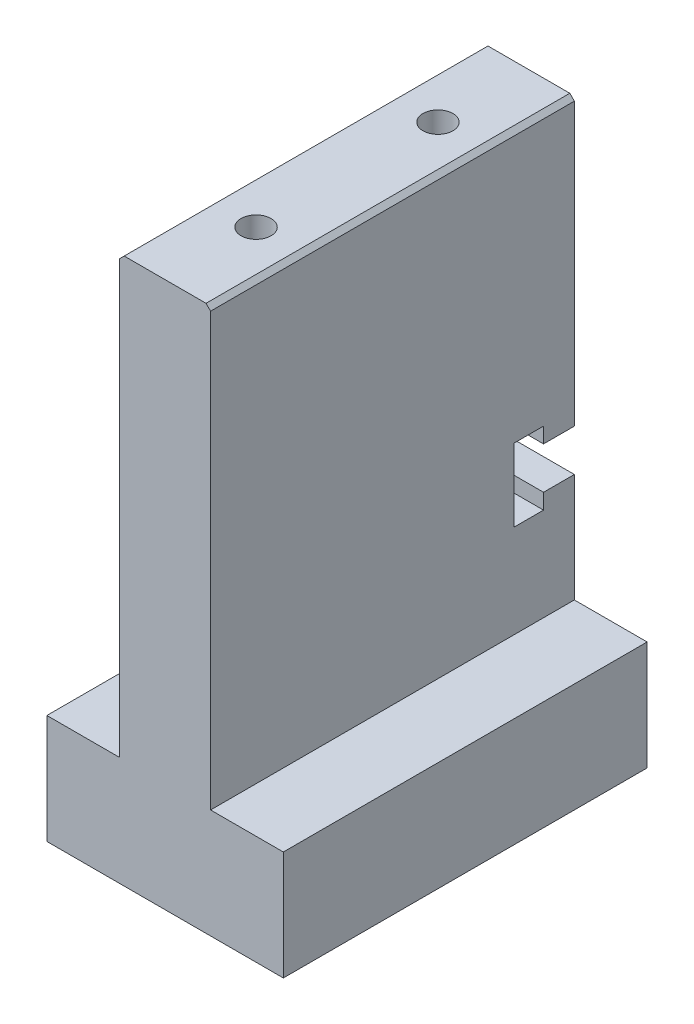
SolidWorks part; units mm, degrees
ref_plane "Front Plane" through (0, 0, 0) normal (0, 0, 1) x (1, 0, 0)
ref_plane "Top Plane" through (0, 0, 0) normal (0, 1, 0) x (1, 0, 0)
ref_plane "Right Plane" through (0, 0, 0) normal (1, 0, 0) x (0, 0, -1)
sketch "Sketch1" plane through (0, 0, 0) normal (0, 0, 1) x (1, 0, 0)
  line L1 (-10.8894, 5.2918) -> (15.1106, 5.2918)
  line L2 (-10.8894, 5.2918) -> (-10.8894, -6.7082)
  line L3 (-10.8894, -6.7082) -> (15.1106, -6.7082)
  line L4 (15.1106, 5.2918) -> (15.1106, -6.7082)
  dimension "D1" = 26
  dimension "D2" = 12
extrude "Boss-Extrude1" add sketch "Sketch1" along normal blind 40
sketch "Sketch2" plane through (0, 5.2918, 0) normal (0, 1, 0) x (1, 0, 0)
  line L0 (15.1106, 0) -> (-10.8894, 0) construction
  line L1 (-2.8894, 0) -> (7.1106, 0)
  line L2 (-2.8894, 0) -> (-2.8894, -40)
  line L3 (-2.8894, -40) -> (7.1106, -40)
  line L4 (7.1106, 0) -> (7.1106, -40)
  line L5 (15.1106, -40) -> (-10.8894, -40) construction
  line L6 (-10.8894, -40) -> (-10.8894, 0) construction
  dimension "D1" = 8
  dimension "D2" = 10
extrude "Boss-Extrude2" add sketch "Sketch2" along normal blind 48
sketch "Sketch3" plane through (-2.8894, 0, 0) normal (-1, 0, 0) x (0, 0, 1)
  line L0 (0, 53.2918) -> (0, 5.2918) construction
  line L1 (0, 21.8418) -> (3.3898, 21.8418)
  line L2 (0, 21.8418) -> (0, 17.2418)
  line L3 (0, 17.2418) -> (3.3898, 17.2418)
  line L4 (0, 53.2918) -> (40, 53.2918) construction
  line L5 (3.3898, 17.2418) -> (3.3898, 15.5418)
  line L6 (3.3898, 23.5418) -> (6.6639, 23.5418)
  line L7 (3.3898, 23.5418) -> (3.3898, 21.8418)
  line L8 (3.3898, 15.5418) -> (6.6639, 15.5418)
  line L9 (6.6639, 23.5418) -> (6.6639, 15.5418)
  dimension "D1" = 29.75
  dimension "D2" = 31.45
  dimension "D3" = 36.05
  dimension "D4" = 37.75
extrude "Cut-Extrude1" cut sketch "Sketch3" against normal blind 48
hole_wizard "M3 Tapped Hole1" positions "Sketch5" profile "Sketch4" tap size "M3" standard "ISO"
sketch "Sketch5" plane through (0, 0, 0) normal (0, 0, -1) x (-1, 0, 0)
  line L0 (10.8894, -6.7082) -> (-15.1106, -6.7082) construction
  line L1 (-15.1106, -6.7082) -> (-15.1106, 5.2918) construction
  line L2 (-7.1106, 53.2918) -> (2.8894, 53.2918) construction
  line L3 (-7.1106, 53.2918) -> (-7.1106, 21.8418) construction
  point P0 (-9.1106, -0.7082)
  point P2 (4.8894, -0.7082)
  point P4 (-2.1106, 51.2918)
  dimension "D1" = 6
  dimension "D2" = 6
  dimension "D3" = 6
  dimension "D4" = 14
  dimension "D5" = 2
  dimension "D6" = 5
sketch "Sketch4" plane through (9.1106, -0.7082, 0) normal (1, 0, 0) x (0, 1, 0)
  line L0 (0, 0) -> (0, 6.7511)
  line L1 (0, 6.7511) -> (1.25, 6)
  line L2 (1.25, 6) -> (1.25, 0)
  line L5 (1.25, 0) -> (0, 0)
  line L10 (0, 6.7511) -> (-1.25, 6) construction
  line L11 (0, -6.35) -> (0, 107.95) construction
  dimension "Tap Drill Dia." = 2.5
  dimension "Tap Drill Depth" = 6
  dimension "Drill Angle" = 118
cosmetic thread "Hole Thread1" parameters "D1"=6, "D2"=3
cosmetic thread "Hole Thread2" parameters "D1"=6, "D2"=3
cosmetic thread "Hole Thread3" parameters "D1"=6, "D2"=3
hole_wizard "M4 Tapped Hole1" positions "Sketch6" profile "Sketch7" tap size "M4" standard "ISO"
sketch "Sketch6" plane through (0, 53.2918, 0) normal (0, 1, 0) x (1, 0, 0)
  line L0 (7.1106, 0) -> (-2.8894, 0) construction
  point P0 (2.1106, -10)
  point P2 (2.1106, -30)
  point P5 (2.1106, 0)
  dimension "D1" = 10
  dimension "D2" = 20
sketch "Sketch7" plane through (2.1106, 53.2918, 10) normal (1, 0, 0) x (0, 0, 1)
  line L0 (0, 0) -> (0, 8.9914)
  line L1 (0, 8.9914) -> (1.65, 8)
  line L2 (1.65, 8) -> (1.65, 0)
  line L5 (1.65, 0) -> (0, 0)
  line L10 (0, 8.9914) -> (-1.65, 8) construction
  line L11 (0, -6.35) -> (0, 107.95) construction
  dimension "Tap Drill Dia." = 3.3
  dimension "Tap Drill Depth" = 8
  dimension "Drill Angle" = 118
cosmetic thread "Hole Thread4" parameters "D1"=8, "D2"=4
cosmetic thread "Hole Thread5" parameters "D1"=8, "D2"=4
chamfer "Chamfer1" distance 0.5 angle 45 2 edges at (7.1106, 53.2918, 20) (-2.8894, 53.2918, 20)
